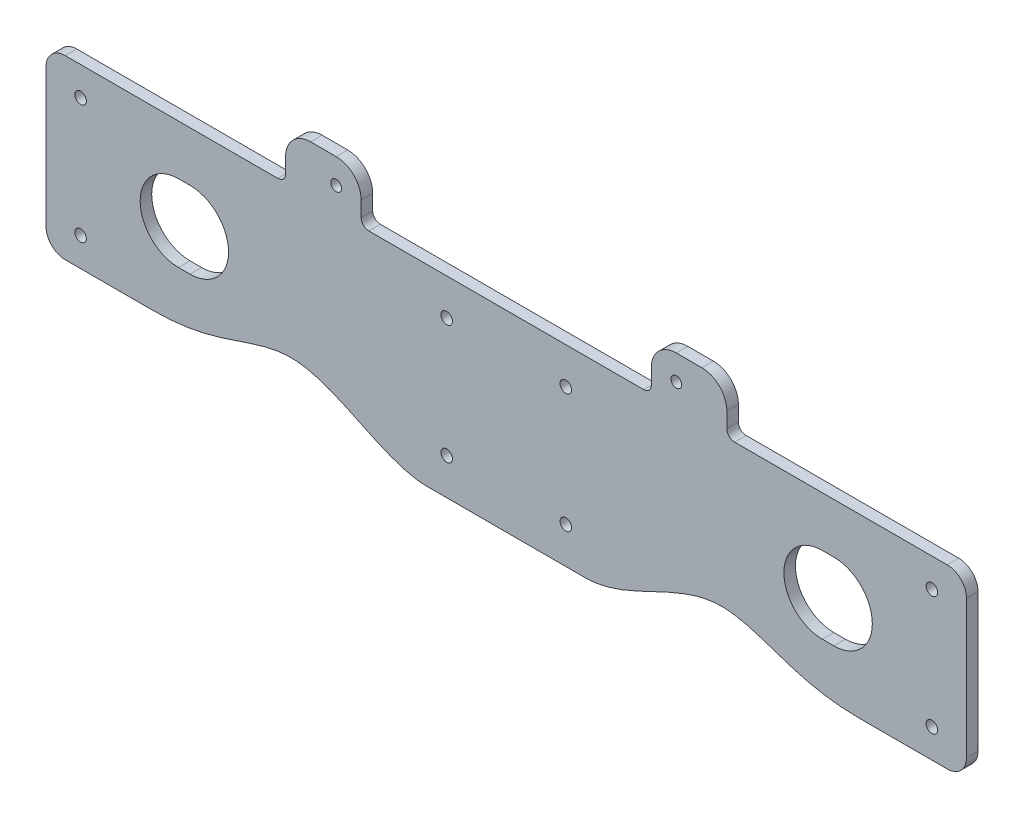
SolidWorks part; units mm, degrees
ref_plane "Front Plane" through (0, 0, 0) normal (0, 0, 1) x (1, 0, 0)
ref_plane "Top Plane" through (0, 0, 0) normal (0, 1, 0) x (1, 0, 0)
ref_plane "Right Plane" through (0, 0, 0) normal (1, 0, 0) x (0, 0, -1)
sketch "Sketch1" plane through (0, 0, 0) normal (0, 0, 1) x (1, 0, 0)
  line L0 (119.75, 0) -> (119.75, 80) construction
  line L1 (0, 0) -> (119.75, 0)
  line L2 (0, 0) -> (0, 50)
  line L3 (0, 50) -> (119.75, 50)
  line L4 (119.75, 0) -> (119.75, 50)
  dimension "D1" = 119.75
  dimension "D2" = 50
  dimension "D3" = 80
extrude "Boss-Extrude1" add sketch "Sketch1" along normal blind 3
sketch "Sketch2" plane through (0, 0, 0) normal (0, 0, -1) x (-1, 0, 0)
  line L0 (-119.75, 0) -> (-119.75, 50) construction
  line L1 (-119.75, 50) -> (0, 50) construction
  line L2 (0, 50) -> (0, 0) construction
  line L3 (0, 0) -> (-119.75, 0) construction
  circle A0 centre (-104.25, 40.5) radius 1.5
  circle A1 centre (-104.25, 9.5) radius 1.5
  circle A2 centre (-9, 42.5) radius 1.5
  circle A3 centre (-9, 11.5) radius 1.5
  point P16 (-96.1222, 50)
  dimension "D9" = 3
  dimension "D10" = 3
  dimension "D11" = 3
  dimension "D12" = 3
  dimension "D1" = 15.5
  dimension "D2" = 9.5
  dimension "D3" = 31
  dimension "D4" = 15.5
  dimension "D5" = 9
  dimension "D6" = 7.5
  dimension "D7" = 9
  dimension "D8" = 11.5
extrude "Cut-Extrude1" cut sketch "Sketch2" against normal blind 3
mirror "Mirror1" about plane through (119.75, 0, 3) normal (-1, 0, 0) of bodies 102
sketch "Sketch3" plane through (0, 0, 0) normal (0, 0, -1) x (-1, 0, 0)
  line L0 (-239.5, 50) -> (0, 50) construction
  line L1 (-82, 50) -> (-82, 56)
  line L2 (-82, 56) -> (-62.3438, 56) construction
  line L3 (-75.5, 62.5) -> (-68.8438, 62.5)
  line L4 (-82, 50) -> (-62.3438, 50)
  line L6 (-62.3438, 56) -> (-62.3438, 50)
  line L7 (0, 50) -> (0, 0) construction
  arc A0 (-82, 56) -> (-75.5, 62.5) centre (-75.5, 56) cw
  arc A1 (-68.8438, 62.5) -> (-62.3438, 56) centre (-68.8438, 56) cw
  circle A2 centre (-75.5, 56) radius 1.4
  dimension "D4" = 6.5
  dimension "D5" = 6.5
  dimension "D6" = 2.8
  dimension "D1" = 62.3438
  dimension "D2" = 19.6562
  dimension "D3" = 12.5
extrude "Boss-Extrude2" add sketch "Sketch3" against normal up to surface (3 mm away) up to face at (7.5, 11.5, 3)
ref_plane "Plane1" through (119.75, 0, 0) normal (1, 0, 0) x (0, 0, -1)
mirror "Mirror2" about plane through (119.75, 0, 0) normal (1, 0, 0) of "Boss-Extrude2"
fillet "Fillet1" radius 2 4 edges at (177.1562, 50, 1.5) (157.5, 50, 1.5)
sketch "Sketch4" plane through (0, 0, 0) normal (0, 0, -1) x (-1, 0, 0)
  line L0 (0, 0) -> (-239.5, 0) construction
  line L1 (-167.1959, 0) -> (-174.2238, 0) construction
  line L3 (-27.6551, 4) -> (0, 4)
  line L4 (0, 50) -> (0, 0) construction
  line L5 (0, 4) -> (0, 0)
  line L6 (0, 0) -> (-99.2562, 0)
  spline S0 degree 3 poles (-99.2562, 0) (-90.1166, 0) (-79.0053, 8.4492) (-62.7368, 12.1526) (-50.6251, 8.6725) (-38.7019, 4) (-27.6551, 4) knots 0 0 0 0 0.434614 0.535271 0.727022 1 1 1 1
  dimension "D1" = 4
extrude "Cut-Extrude2" cut sketch "Sketch4" against normal blind 10
mirror "Mirror3" about plane through (119.75, 0, 0) normal (1, 0, 0) of "Cut-Extrude2"
fillet "Fillet2" radius 5 4 edges at (239.5, 4, 1.5) (239.5, 50, 1.5) (0, 4, 1.5) (0, 50, 1.5)
sketch "Sketch5" plane through (0, 0, 0) normal (0, 0, -1) x (-1, 0, 0)
  line L0 (-34.5, 27) -> (-37.5, 27) construction
  line L1 (-34.5, 17) -> (-37.5, 17)
  line L2 (-34.5, 37) -> (-37.5, 37)
  arc A0 (-34.5, 17) -> (-34.5, 37) centre (-34.5, 27) ccw
  arc A1 (-37.5, 37) -> (-37.5, 17) centre (-37.5, 27) ccw
  point P4 (-36, 27)
  dimension "D1" = 10
extrude "Cut-Extrude3" cut sketch "Sketch5" against normal blind 10
mirror "Mirror4" about plane through (119.75, 0, 0) normal (1, 0, 0) of "Cut-Extrude3"
